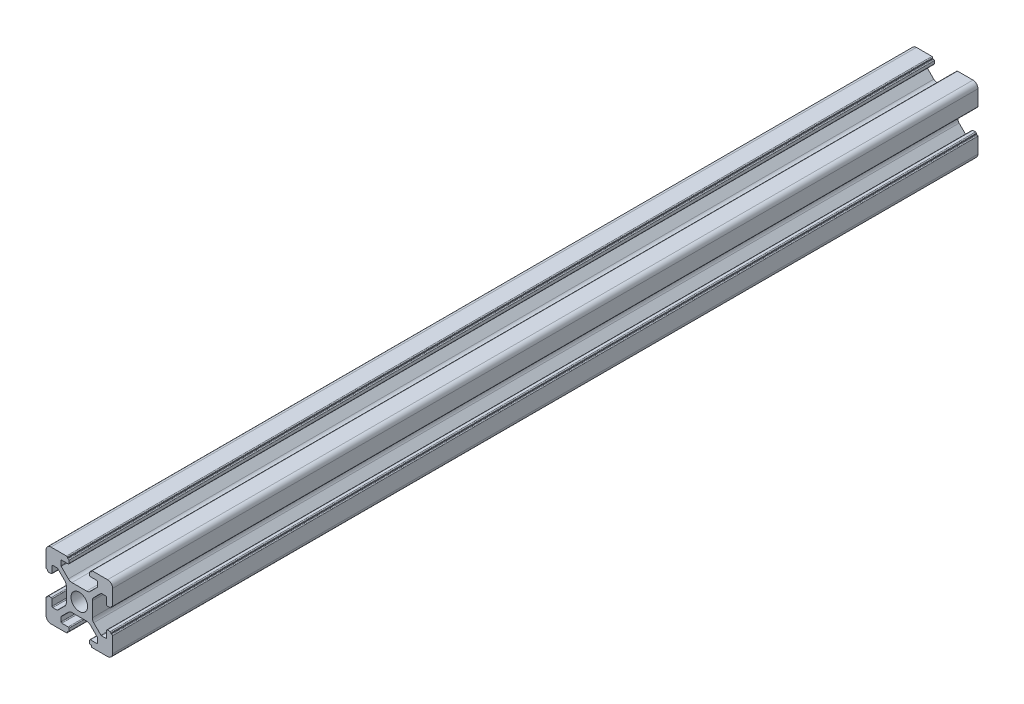
SolidWorks part; units mm, degrees
ref_plane "前视基准面" through (0, 0, 0) normal (0, 0, 1) x (1, 0, 0)
ref_plane "上视基准面" through (0, 0, 0) normal (0, 1, 0) x (1, 0, 0)
ref_plane "右视基准面" through (0, 0, 0) normal (1, 0, 0) x (0, 0, -1)
sketch "草图1" plane through (0, 0, 0) normal (0, 0, 1) x (1, 0, 0)
  line L0 (0, 0) -> (0, 5.5) construction
  line L1 (-8.5023, -10.0023) -> (-3.85, -10.0023)
  line L2 (-10.0023, -8.5023) -> (-10.0023, -3.85)
  line L3 (-8.5023, 10.0023) -> (-3.85, 10.0023)
  line L4 (10.0023, -8.5023) -> (10.0023, -3.85)
  line L5 (-10.0023, -10.0023) -> (10.0023, 10.0023) construction
  line L6 (-10.0023, 10.0023) -> (10.0023, -10.0023) construction
  line L7 (-2.218, -3.9) -> (2.218, -3.9)
  line L8 (-3.9, -2.218) -> (-3.9, 2.218)
  line L9 (-2.218, 3.9) -> (2.218, 3.9)
  line L10 (3.9, -2.218) -> (3.9, 2.218)
  line L11 (-3.9, -3.9) -> (3.9, 3.9) construction
  line L12 (-3.9, 3.9) -> (3.9, -3.9) construction
  line L13 (-5.25, -8.2) -> (-3.35, -8.2)
  line L14 (-8.2, -5.25) -> (-8.2, -3.35)
  line L15 (-5.25, 8.2) -> (-3.35, 8.2)
  line L16 (8.2, -5.25) -> (8.2, -3.35)
  line L17 (-8.2, -8.2) -> (8.2, 8.2) construction
  line L18 (-8.2, 8.2) -> (8.2, -8.2) construction
  line L19 (-7.95, 5.5) -> (-6.6642, 5.5)
  line L20 (0, 0) -> (5.5, 0) construction
  line L23 (-5.5, 7.95) -> (-5.5, 6.6642)
  line L26 (0, 0) -> (-0.5303, 0.5303)
  line L27 (3.2787, 4.3393) -> (5.4268, 6.4874)
  line L28 (0, 0) -> (0.5303, -0.5303)
  line L29 (5.5, 6.6642) -> (5.5, 7.95)
  line L30 (4.3393, 3.2787) -> (6.4874, 5.4268)
  line L31 (6.6642, 5.5) -> (7.95, 5.5)
  line L32 (4.3393, -3.2787) -> (6.4874, -5.4268)
  line L33 (3.2787, -4.3393) -> (5.4268, -6.4874)
  line L34 (-3.2787, -4.3393) -> (-5.4268, -6.4874)
  line L35 (-4.3393, -3.2787) -> (-6.4874, -5.4268)
  line L36 (-4.3393, 3.2787) -> (-6.4874, 5.4268)
  line L37 (-3.2787, 4.3393) -> (-5.4268, 6.4874)
  line L38 (3.1, -8.45) -> (3.1, -9.2523)
  line L39 (8.45, 3.1) -> (9.2523, 3.1)
  line L40 (-5.5, -6.6642) -> (-5.5, -7.95)
  line L41 (-6.6642, -5.5) -> (-7.95, -5.5)
  line L42 (5.5, -6.6642) -> (5.5, -7.95)
  line L43 (6.6642, -5.5) -> (7.95, -5.5)
  line L44 (9.2523, -3.1) -> (8.45, -3.1)
  line L46 (10.0023, 3.85) -> (10.0023, 8.5023)
  line L47 (8.2, 3.35) -> (8.2, 5.25)
  line L48 (-3.1, -9.2523) -> (-3.1, -8.45)
  line L49 (-8.45, -3.1) -> (-9.2523, -3.1)
  line L50 (-9.2523, 3.1) -> (-8.45, 3.1)
  line L51 (-3.1, 8.45) -> (-3.1, 9.2523)
  line L52 (3.1, 9.2523) -> (3.1, 8.45)
  line L53 (3.85, 10.0023) -> (8.5023, 10.0023)
  line L54 (3.35, 8.2) -> (5.25, 8.2)
  line L55 (-10.0023, 3.85) -> (-10.0023, 8.5023)
  line L56 (-8.2, 3.35) -> (-8.2, 5.25)
  line L57 (3.35, -8.2) -> (5.25, -8.2)
  line L58 (3.85, -10.0023) -> (8.5023, -10.0023)
  line L59 (9.7523, -3.6) -> (9.5023, -3.6)
  line L61 (9.7523, 3.6) -> (9.5023, 3.6)
  line L62 (9.5023, -3.6) -> (9.5023, -3.35)
  line L63 (3.6, -9.7523) -> (3.6, -9.5023)
  line L64 (3.35, -9.5023) -> (3.6, -9.5023)
  line L65 (9.5023, 3.35) -> (9.5023, 3.6)
  line L66 (-3.6, -9.5023) -> (-3.35, -9.5023)
  line L67 (-3.6, -9.7523) -> (-3.6, -9.5023)
  line L68 (-9.7523, -3.6) -> (-9.5023, -3.6)
  line L69 (-9.5023, -3.35) -> (-9.5023, -3.6)
  line L70 (-9.5023, 3.6) -> (-9.5023, 3.35)
  line L71 (-9.7523, 3.6) -> (-9.5023, 3.6)
  line L72 (-3.6, 9.7523) -> (-3.6, 9.5023)
  line L73 (-3.35, 9.5023) -> (-3.6, 9.5023)
  line L74 (3.6, 9.5023) -> (3.35, 9.5023)
  line L75 (3.6, 9.7523) -> (3.6, 9.5023)
  circle A0 centre (0, 0) radius 2.5
  arc A1 (10.0023, 8.5023) -> (8.5023, 10.0023) centre (8.5023, 8.5023) ccw
  arc A2 (8.5023, -10.0023) -> (10.0023, -8.5023) centre (8.5023, -8.5023) ccw
  arc A3 (-10.0023, -8.5023) -> (-8.5023, -10.0023) centre (-8.5023, -8.5023) ccw
  arc A4 (-10.0023, 8.5023) -> (-8.5023, 10.0023) centre (-8.5023, 8.5023) cw
  arc A5 (-9.5023, -3.35) -> (-9.2523, -3.1) centre (-9.2523, -3.35) cw
  arc A6 (-9.7523, -3.6) -> (-10.0023, -3.85) centre (-9.7523, -3.85) ccw
  arc A7 (-8.45, -3.1) -> (-8.2, -3.35) centre (-8.45, -3.35) cw
  arc A8 (-7.95, -5.5) -> (-8.2, -5.25) centre (-7.95, -5.25) cw
  arc A9 (-6.4874, -5.4268) -> (-6.6642, -5.5) centre (-6.6642, -5.25) cw
  arc A10 (-5.4268, -6.4874) -> (-5.5, -6.6642) centre (-5.25, -6.6642) ccw
  arc A11 (-5.5, -7.95) -> (-5.25, -8.2) centre (-5.25, -7.95) ccw
  arc A12 (-3.6, -9.7523) -> (-3.85, -10.0023) centre (-3.85, -9.7523) cw
  arc A13 (-3.35, -9.5023) -> (-3.1, -9.2523) centre (-3.35, -9.2523) ccw
  arc A14 (-3.1, -8.45) -> (-3.35, -8.2) centre (-3.35, -8.45) ccw
  arc A15 (3.1, -8.45) -> (3.35, -8.2) centre (3.35, -8.45) cw
  arc A16 (5.5, -7.95) -> (5.25, -8.2) centre (5.25, -7.95) cw
  arc A17 (5.4268, -6.4874) -> (5.5, -6.6642) centre (5.25, -6.6642) cw
  arc A18 (6.4874, -5.4268) -> (6.6642, -5.5) centre (6.6642, -5.25) ccw
  arc A19 (7.95, -5.5) -> (8.2, -5.25) centre (7.95, -5.25) ccw
  arc A20 (8.45, -3.1) -> (8.2, -3.35) centre (8.45, -3.35) ccw
  arc A21 (9.5023, -3.35) -> (9.2523, -3.1) centre (9.2523, -3.35) ccw
  arc A22 (9.7523, -3.6) -> (10.0023, -3.85) centre (9.7523, -3.85) cw
  arc A23 (3.35, -9.5023) -> (3.1, -9.2523) centre (3.35, -9.2523) cw
  arc A24 (3.6, -9.7523) -> (3.85, -10.0023) centre (3.85, -9.7523) ccw
  arc A25 (7.95, 5.5) -> (8.2, 5.25) centre (7.95, 5.25) cw
  arc A26 (8.2, 3.35) -> (8.45, 3.1) centre (8.45, 3.35) ccw
  arc A27 (9.5023, 3.35) -> (9.2523, 3.1) centre (9.2523, 3.35) cw
  arc A28 (9.7523, 3.6) -> (10.0023, 3.85) centre (9.7523, 3.85) ccw
  arc A29 (6.6642, 5.5) -> (6.4874, 5.4268) centre (6.6642, 5.25) ccw
  arc A30 (5.4268, 6.4874) -> (5.5, 6.6642) centre (5.25, 6.6642) ccw
  arc A31 (5.5, 7.95) -> (5.25, 8.2) centre (5.25, 7.95) ccw
  arc A32 (3.1, 8.45) -> (3.35, 8.2) centre (3.35, 8.45) ccw
  arc A33 (3.6, 9.7523) -> (3.85, 10.0023) centre (3.85, 9.7523) cw
  arc A34 (3.35, 9.5023) -> (3.1, 9.2523) centre (3.35, 9.2523) ccw
  arc A35 (-9.7523, 3.6) -> (-10.0023, 3.85) centre (-9.7523, 3.85) cw
  arc A36 (-9.5023, 3.35) -> (-9.2523, 3.1) centre (-9.2523, 3.35) ccw
  arc A37 (-8.45, 3.1) -> (-8.2, 3.35) centre (-8.45, 3.35) ccw
  arc A38 (-8.2, 5.25) -> (-7.95, 5.5) centre (-7.95, 5.25) cw
  arc A39 (-6.4874, 5.4268) -> (-6.6642, 5.5) centre (-6.6642, 5.25) ccw
  arc A40 (-5.4268, 6.4874) -> (-5.5, 6.6642) centre (-5.25, 6.6642) cw
  arc A41 (-5.5, 7.95) -> (-5.25, 8.2) centre (-5.25, 7.95) cw
  arc A42 (-3.1, 8.45) -> (-3.35, 8.2) centre (-3.35, 8.45) cw
  arc A43 (-3.1, 9.2523) -> (-3.35, 9.5023) centre (-3.35, 9.2523) ccw
  arc A44 (-3.6, 9.7523) -> (-3.85, 10.0023) centre (-3.85, 9.7523) ccw
  arc A45 (-4.3393, 3.2787) -> (-3.9, 2.218) centre (-5.4, 2.218) cw
  arc A46 (-3.2787, 4.3393) -> (-2.218, 3.9) centre (-2.218, 5.4) ccw
  arc A47 (3.2787, 4.3393) -> (2.218, 3.9) centre (2.218, 5.4) cw
  arc A48 (4.3393, 3.2787) -> (3.9, 2.218) centre (5.4, 2.218) ccw
  arc A49 (4.3393, -3.2787) -> (3.9, -2.218) centre (5.4, -2.218) cw
  arc A50 (3.2787, -4.3393) -> (2.218, -3.9) centre (2.218, -5.4) ccw
  arc A51 (-4.3393, -3.2787) -> (-3.9, -2.218) centre (-5.4, -2.218) ccw
  arc A52 (-2.218, -3.9) -> (-3.2787, -4.3393) centre (-2.218, -5.4) ccw
  point P0 (0, 0)
  point P7 (10.0023, 0)
  point P62 (0, 0)
  point P76 (0, 0)
  point P92 (-8.2, -5.5)
  point P99 (0, 0)
  point P106 (-5.5, -8.2)
  point P117 (5.5, -8.2)
  point P124 (8.2, -5.5)
  point P137 (8.2, 5.5)
  point P140 (8.2, 3.1)
  point P147 (6.5607, 5.5)
  point P152 (5.5, 8.2)
  point P167 (-8.2, 5.5)
  point P174 (-5.5, 8.2)
  dimension "D1" = 1.5
  dimension "D5" = 0.25
  dimension "D6" = 1.5
  dimension "D2" = 4
  dimension "D3" = 4
  dimension "D4" = 4
extrude "凸台-拉伸1" add sketch "草图1" along normal blind 260 contours A52 L7 A50 L33 A17 L42 A16 L57 A15 L38 A23 L64 L63 A24 L58 A2 L4 A22 L59 L62 A21 L44 A20 L16 A19 L43 A18 L32 A49 L10 A48 L30 A29 L31 A25 L47 A26 L39 A27 L65 L61 A28 L46 A1 L53 A33 L75 L74 A34 L52 A32
